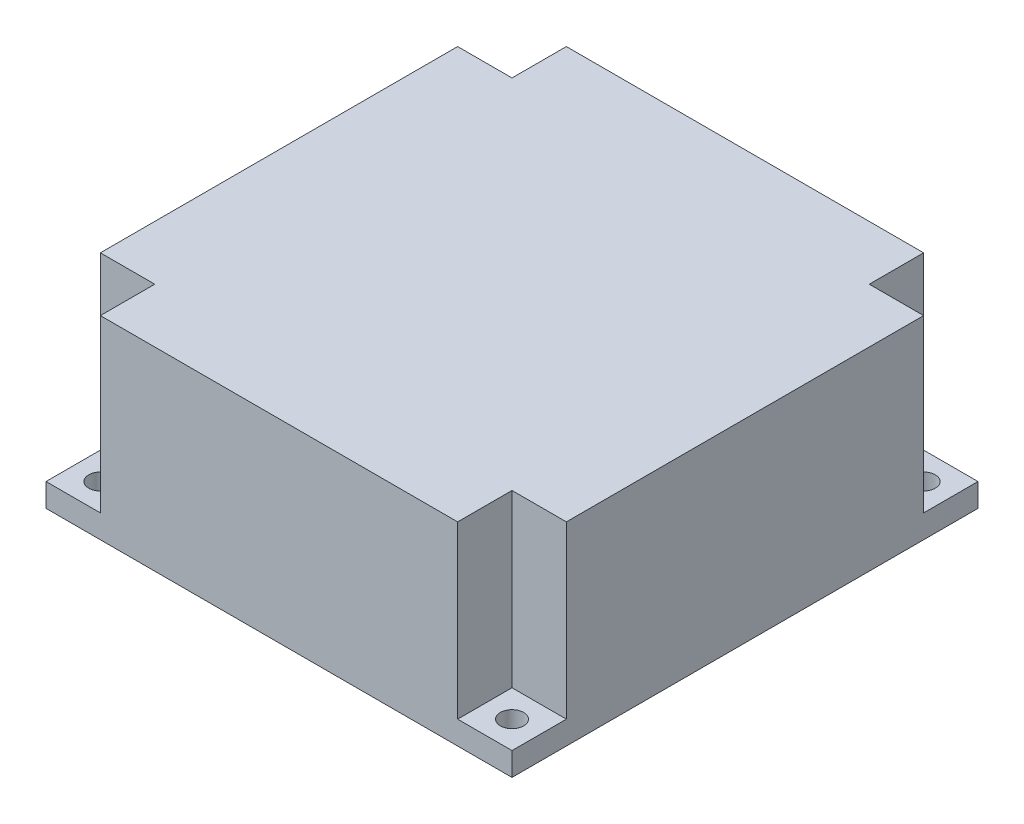
SolidWorks part; units mm, degrees
ref_plane "Front Plane" through (0, 0, 0) normal (0, 0, 1) x (1, 0, 0)
ref_plane "Top Plane" through (0, 0, 0) normal (0, 1, 0) x (1, 0, 0)
ref_plane "Right Plane" through (0, 0, 0) normal (1, 0, 0) x (0, 0, -1)
sketch "Sketch1" plane through (0, 0, 0) normal (0, 1, 0) x (1, 0, 0)
  line L0 (30, 60) -> (30, 0) construction
  line L1 (0, 0) -> (60, 0)
  line L2 (0, 0) -> (0, 60)
  line L3 (0, 60) -> (60, 60)
  line L4 (60, 0) -> (60, 60)
  line L5 (3.5, 3.5) -> (56.5, 56.5) construction
  line L6 (56.5, 56.5) -> (3.5, 56.5) construction
  line L7 (56.5, 56.5) -> (56.5, 3.5) construction
  circle A0 centre (3.5, 3.5) radius 1.5
  circle A1 centre (56.5, 3.5) radius 1.5
  circle A2 centre (56.5, 56.5) radius 1.5
  circle A3 centre (3.5, 56.5) radius 1.5
  point P18 (30, 30)
  dimension "D3" = 3
  dimension "D1" = 60
  dimension "D2" = 60
  dimension "D6" = 53
  dimension "D7" = 53
  dimension "D4" = 2
  dimension "D5" = 2
extrude "Boss-Extrude1" add sketch "Sketch1" along normal blind 3
sketch "Sketch2" plane through (0, 3, 0) normal (0, 1, 0) x (1, 0, 0)
  line L0 (0, 0) -> (60, 0) construction
  line L1 (7, 60) -> (53, 60)
  line L2 (7, 60) -> (7, 53)
  line L3 (7, 0) -> (53, 0)
  line L4 (53, 60) -> (53, 53)
  line L5 (60, 60) -> (0, 60) construction
  line L6 (60, 0) -> (60, 60) construction
  line L7 (0, 60) -> (0, 0) construction
  line L8 (7, 53) -> (0, 53)
  line L9 (60, 53) -> (53, 53)
  line L10 (60, 53) -> (60, 7)
  line L11 (60, 7) -> (53, 7)
  line L12 (0, 53) -> (0, 7)
  line L13 (7, 7) -> (7, 0)
  line L14 (7, 7) -> (0, 7)
  line L15 (53, 7) -> (53, 0)
  point P6 (60, 30)
  dimension "D1" = 7
  dimension "D2" = 7
  dimension "D3" = 7
  dimension "D4" = 7
extrude "Boss-Extrude2" add sketch "Sketch2" along normal blind 22
sketch "Sketch3" plane through (0, 0, 0) normal (0, -1, 0) x (1, 0, 0)
  line L0 (0, -60) -> (60, 0) construction
  point P4 (30, -30)
